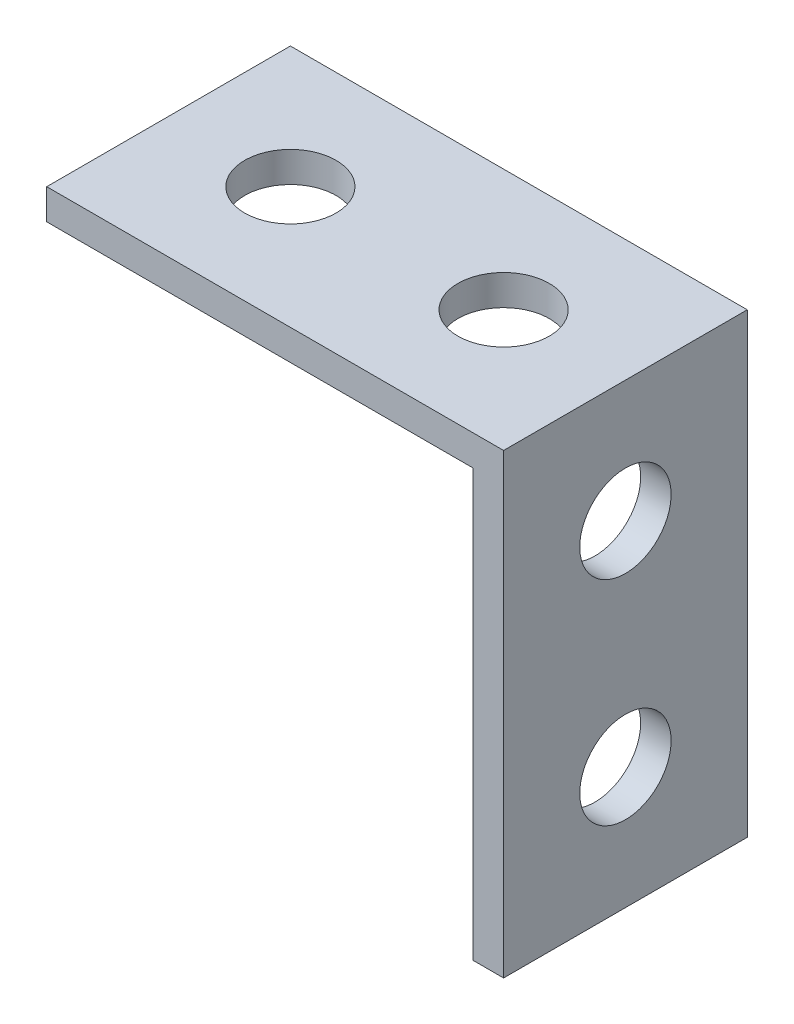
SolidWorks part; units mm, degrees
ref_plane "Front" through (0, 0, 0) normal (0, 0, 1) x (1, 0, 0)
ref_plane "Top" through (0, 0, 0) normal (0, 1, 0) x (1, 0, 0)
ref_plane "Right" through (0, 0, 0) normal (1, 0, 0) x (0, 0, -1)
sketch "Sketch1" plane through (0, 0, 0) normal (0, 0, 1) x (1, 0, 0)
  line L1 (-7.5, 0.5) -> (7.5, 0.5)
  line L2 (-7.5, 0.5) -> (-7.5, -0.5)
  line L3 (-7.5, -0.5) -> (7.5, -0.5)
  line L4 (7.5, 0.5) -> (7.5, -0.5)
  line L5 (-7.5, 0.5) -> (7.5, -0.5) construction
  line L6 (-7.5, -0.5) -> (7.5, 0.5) construction
  line L7 (7.5, -0.5) -> (6.5, -0.5)
  line L8 (7.5, -0.5) -> (7.5, -14.5)
  line L9 (7.5, -14.5) -> (6.5, -14.5)
  line L10 (6.5, -0.5) -> (6.5, -14.5)
  point P0 (0, 0)
  point P9 (0, 0)
  dimension "D1" = 15
  dimension "D2" = 1
  dimension "D3" = 1
  dimension "D4" = 14
extrude "Boss-Extrude1" add sketch "Sketch1" along normal blind 8 contours L4 L1 L2 L3 | L3 L10 L9 L8
sketch "Sketch2" plane through (0, 0.5, 0) normal (0, 1, 0) x (1, 0, 0)
  line L0 (-7.5, -8) -> (-7.5, 0) construction
  line L1 (7.5, -8) -> (7.5, 0) construction
  circle A0 centre (-3.5, -4) radius 1.5
  circle A1 centre (3.5, -4) radius 1.5
  point P6 (0, 0)
  dimension "D1" = 3
  dimension "D2" = 4
  dimension "D3" = 4
extrude "Cut-Extrude1" cut sketch "Sketch2" against normal through all contours A0 | A1
sketch "Sketch3" plane through (7.5, 0, 0) normal (1, 0, 0) x (0, 0, -1)
  line L0 (-8, 0.5) -> (0, 0.5) construction
  line L1 (-8, -14.5) -> (0, -14.5) construction
  circle A0 centre (-4, -3.5) radius 1.5
  circle A1 centre (-4, -10.5) radius 1.5
  point P8 (0, 0)
  point P9 (0, 0)
  point P10 (0, 0)
  dimension "D1" = 3
  dimension "D2" = 4
  dimension "D3" = 4
extrude "Cut-Extrude2" cut sketch "Sketch3" against normal through all
